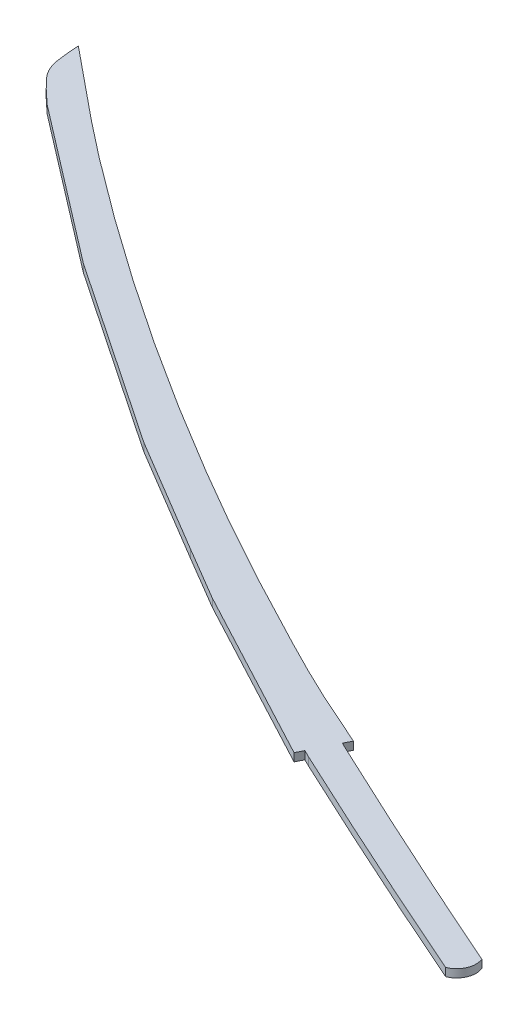
SolidWorks part; units mm, degrees
ref_plane "Front Plane" through (0, 0, 0) normal (0, 0, 1) x (1, 0, 0)
ref_plane "Top Plane" through (0, 0, 0) normal (0, 1, 0) x (1, 0, 0)
ref_plane "Right Plane" through (0, 0, 0) normal (1, 0, 0) x (0, 0, -1)
sketch "Sketch1" plane through (0, 0, 0) normal (0, 1, 0) x (1, 0, 0)
  line L0 (146.0811, -290.4497) -> (812.7477, -290.4497) construction
  line L1 (0, 0) -> (914.4, 0)
  line L2 (0, 0) -> (0, -609.6)
  line L3 (0, -609.6) -> (914.4, -609.6)
  line L5 (155.6469, -285.0942) -> (774.3136, -285.0942) construction
  line L13 (402.2954, -312.3372) -> (311.1038, -257.941)
  line L14 (311.1038, -257.941) -> (164.7409, -159.3288)
  line L15 (164.7409, -159.3288) -> (42.0355, -65.1986)
  line L39 (914.4, 0) -> (914.4, -609.6)
  line L40 (582.4443, -410.6991) -> (585.2626, -404.9825)
  line L44 (402.2954, -312.3372) -> (444.6581, -337.3691)
  line L46 (557.2504, -361.2113) -> (597.9158, -379.3167)
  line L49 (585.6986, -404.0981) -> (594.6615, -385.9177) construction
  line L50 (595.055, -385.1195) -> (597.9158, -379.3167)
  line L51 (898.5266, -511.0935) -> (892.6644, -524.9678) construction
  line L52 (882.7852, -548.3494) -> (891.9789, -552.234) construction
  line L53 (595.055, -385.1195) -> (601.0818, -388.0907)
  line L54 (585.2626, -404.9825) -> (591.0367, -407.8291)
  line L55 (585.2626, -404.9825) -> (585.6986, -404.0981) construction
  line L56 (594.6615, -385.9177) -> (595.055, -385.1195) construction
  line L57 (801.5635, -469.1126) -> (797.7435, -477.838)
  line L58 (797.7435, -477.838) -> (789.0624, -497.6664) construction
  line L59 (789.0624, -497.6664) -> (785.2423, -506.3918)
  line L60 (892.6644, -524.9678) -> (888.6474, -534.4751) construction
  line L61 (888.6474, -534.4751) -> (882.7852, -548.3494) construction
  arc A2 (605.1496, -379.478) -> (898.5266, -511.0935) centre (4120.06, 7062.6405) ccw construction
  arc A3 (882.7852, -548.3494) -> (586.9872, -416.4504) centre (4086.1161, 7033.1013) cw construction
  arc A4 (898.5266, -511.0935) -> (882.7852, -548.3494) centre (877.3816, -524.1127) cw construction
  arc A5 (601.0818, -388.0907) -> (797.7435, -477.838) centre (4120.06, 7062.6405) ccw
  arc A6 (891.6253, -518.508) -> (892.6644, -524.9678) centre (877.3816, -524.1127) cw construction
  arc A7 (789.0624, -497.6664) -> (591.0367, -407.8291) centre (4086.1161, 7033.1013) cw
  arc A8 (797.7435, -477.838) -> (789.0624, -497.6664) centre (783.4887, -483.4117) cw
  arc A9 (797.7435, -477.838) -> (891.6253, -518.508) centre (4120.06, 7062.6405) ccw construction
  arc A10 (601.0818, -388.0907) -> (891.6253, -518.508) centre (4120.06, 7062.6405) ccw construction
  arc A11 (883.3038, -538.2274) -> (789.0624, -497.6664) centre (4086.1161, 7033.1013) cw construction
  arc A12 (883.3038, -538.2274) -> (591.0367, -407.8291) centre (4086.1161, 7033.1013) cw construction
  arc A13 (892.6644, -524.9678) -> (888.6474, -534.4751) centre (877.3816, -524.1127) cw construction
  arc A14 (888.6474, -534.4751) -> (883.3038, -538.2274) centre (877.3816, -524.1127) cw construction
  arc A15 (891.6253, -518.508) -> (883.3038, -538.2274) centre (877.3816, -524.1127) cw construction
  spline S0 degree 3 poles (14.2196, -12.7545) (41.2191, -34.5525) (67.6638, -57.0562) (95.2181, -78.1483) (189.4496, -150.2802) (288.8784, -215.4599) (391.8905, -274.3336) (427.5283, -294.7015) (463.7316, -314.0882) (500.2159, -332.8978) (519.0572, -342.6115) (537.9582, -352.3822) (557.2504, -361.2113) knots 0 0 0 0 1 1 1 2 2 2 3 3 3 3.591985 3.591985 3.591985 3.591985
  spline S1 degree 1 poles (444.6581, -337.3691) (582.4443, -410.6991) knots 0 0 1 1
  spline S2 degree 3 poles (42.0355, -65.1986) (34.8093, -57.7834) (26.0366, -51.6099) (20.3567, -42.9529) (14.7219, -34.3645) (15.1679, -22.9825) (14.2196, -12.7545) knots 0 0 0 0 1 1 1 2 2 2 2
  point P10 (898.5266, -511.0935)
  point P11 (882.7852, -548.3494)
  point P13 (586.9872, -416.4504)
  point P15 (605.1496, -379.478)
  point P42 (801.5635, -469.1126)
  point P44 (797.7435, -477.838)
  point P45 (789.0624, -497.6664)
  dimension "D3" = 9.525
  dimension "D1" = 914.4
  dimension "D2" = 609.6
  dimension "D4" = 215.9
extrude "Boss-Extrude1" add sketch "Sketch1" along normal blind 6.35
